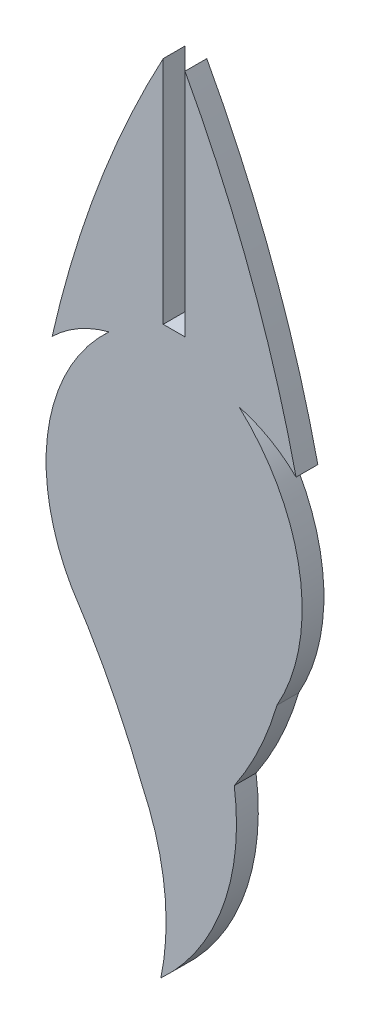
SolidWorks part; units mm, degrees
ref_plane "Front Plane" through (0, 0, 0) normal (0, 0, 1) x (1, 0, 0)
ref_plane "Top Plane" through (0, 0, 0) normal (0, 1, 0) x (1, 0, 0)
ref_plane "Right Plane" through (0, 0, 0) normal (1, 0, 0) x (0, 0, -1)
sketch "Sketch1" plane through (0, 0, 0) normal (0, 0, 1) x (1, 0, 0)
  line L0 (-1.524, -34.6762) -> (0, -34.6762)
  line L1 (0, -34.6762) -> (0, -18.5816)
  line L2 (-0.762, -34.6762) -> (-0.762, -15.1233) construction
  line L3 (-1.524, -18.5816) -> (-1.524, -34.6762)
  arc A0 (0, -18.5816) -> (7.7665, -39.2884) centre (-71.9693, -57.3849) cw
  arc A1 (7.7665, -39.2884) -> (3.7848, -37.0261) centre (1.4811, -45.7156) ccw
  arc A2 (3.7848, -37.0261) -> (6.4293, -53.7715) centre (-5.4496, -47.0659) cw
  arc A3 (6.4293, -53.7715) -> (3.4455, -60.1289) centre (-15.5241, -47.3469) cw
  arc A4 (-3.0015, -63.3324) -> (-7.9533, -53.7715) centre (-50.3528, -81.7941) ccw
  arc A5 (-5.3088, -37.0261) -> (-7.9533, -53.7715) centre (3.9256, -47.0659) ccw
  arc A6 (-9.2905, -39.2884) -> (-5.3088, -37.0261) centre (-3.0051, -45.7156) cw
  arc A7 (-1.524, -18.5816) -> (-9.2905, -39.2884) centre (70.4453, -57.3849) ccw
  arc A8 (-3.0015, -63.3324) -> (-1.6874, -74.3473) centre (-18.7415, -70.796) cw
  arc A9 (-1.6874, -74.3473) -> (3.4455, -60.1289) centre (-12.595, -62.3739) ccw
extrude "Boss-Extrude1" add sketch "Sketch1" along normal blind 1.524
